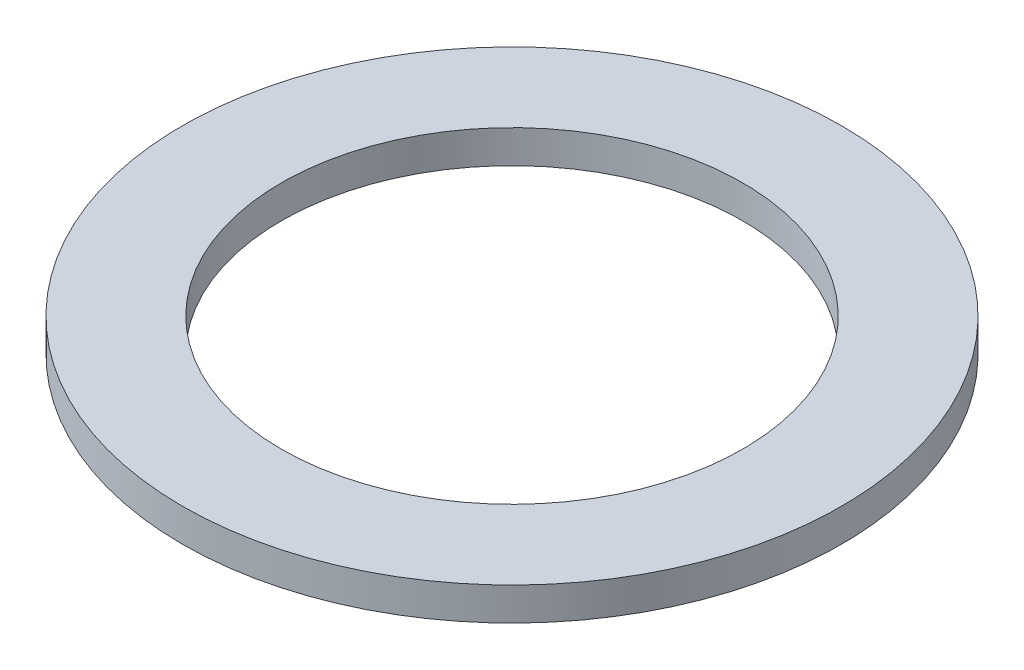
SolidWorks part; units mm, degrees
ref_plane "Front Plane" through (0, 0, 0) normal (0, 0, 1) x (1, 0, 0)
ref_plane "Top Plane" through (0, 0, 0) normal (0, 1, 0) x (1, 0, 0)
ref_plane "Right Plane" through (0, 0, 0) normal (1, 0, 0) x (0, 0, -1)
sketch "Sketch1" plane through (0, 0, 0) normal (0, 1, 0) x (1, 0, 0)
  circle A0 centre (0, 0) radius 10
  dimension "OD" = 20
extrude "Boss-Extrude1" add sketch "Sketch1" along normal blind 1
sketch "Sketch5" plane through (0, 1, 0) normal (0, 1, 0) x (-1, 0, 0)
  circle A0 centre (0, 0) radius 7
  dimension "ID" = 14
extrude "Cut-Extrude1" cut sketch "Sketch5" against normal through all
